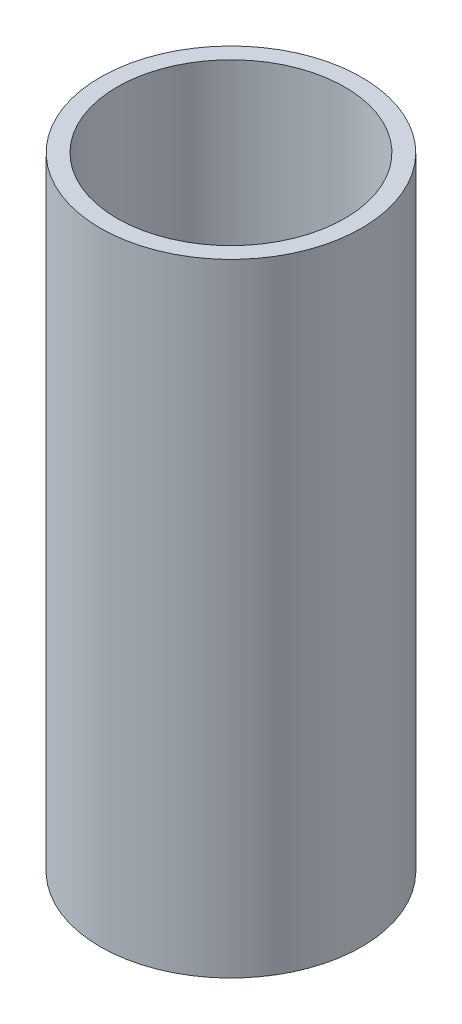
SolidWorks part; units mm, degrees
ref_plane "Front Plane" through (0, 0, 0) normal (0, 0, 1) x (1, 0, 0)
ref_plane "Top Plane" through (0, 0, 0) normal (0, 1, 0) x (1, 0, 0)
ref_plane "Right Plane" through (0, 0, 0) normal (1, 0, 0) x (0, 0, -1)
sketch "Sketch1" plane through (0, 0, 0) normal (0, 1, 0) x (1, 0, 0)
  circle A0 centre (0, 0) radius 10.5
  circle A1 centre (0, 0) radius 9.1466
extrude "Boss-Extrude1" add sketch "Sketch1" along normal blind 50
